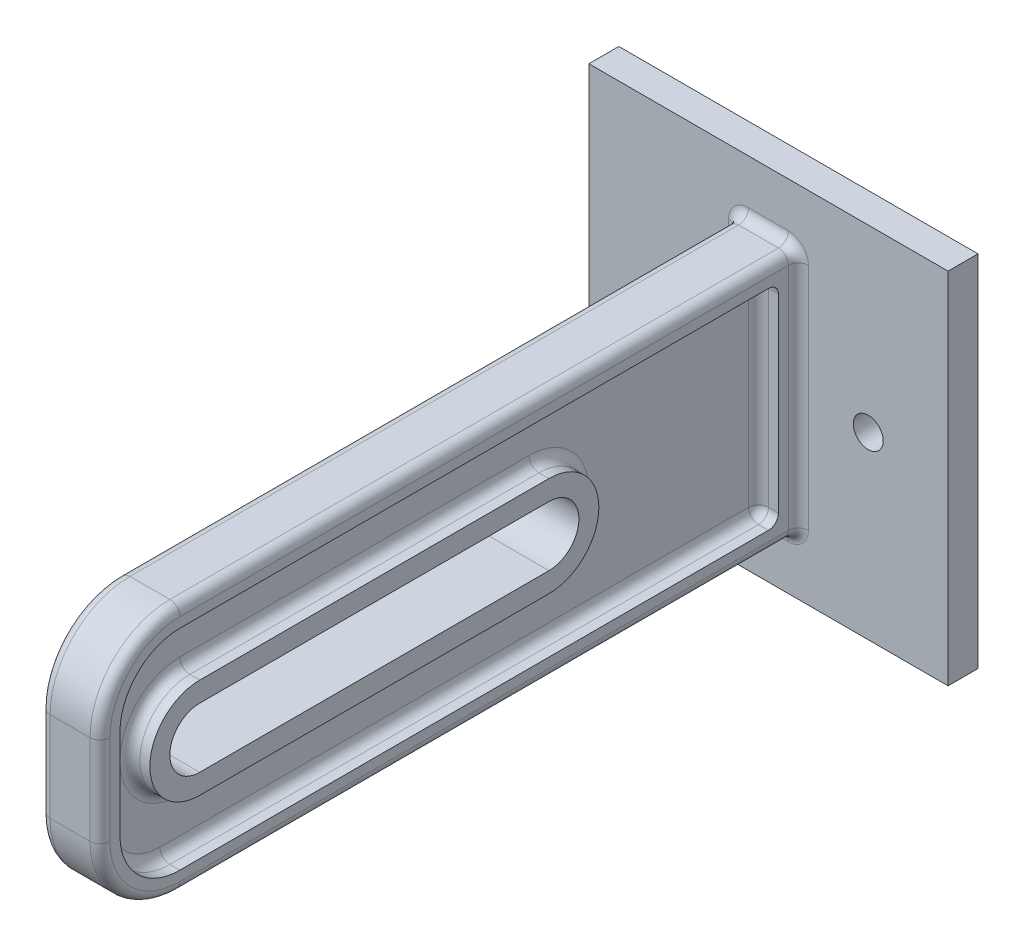
SolidWorks part; units mm, degrees
ref_plane "Front Plane" through (0, 0, 0) normal (0, 0, 1) x (1, 0, 0)
ref_plane "Top Plane" through (0, 0, 0) normal (0, 1, 0) x (1, 0, 0)
ref_plane "Right Plane" through (0, 0, 0) normal (1, 0, 0) x (0, 0, -1)
sketch "Sketch1" plane through (0, 0, 0) normal (0, 0, 1) x (1, 0, 0)
  line L1 (-18, -18) -> (18, -18)
  line L2 (-18, -18) -> (-18, 18)
  line L3 (-18, 18) -> (18, 18)
  line L4 (18, -18) -> (18, 18)
  line L5 (-18, -18) -> (18, 18) construction
  line L6 (-18, 18) -> (18, -18) construction
  point P0 (0, 0)
  dimension "D1" = 36
extrude "Boss-Extrude1" add sketch "Sketch1" along normal blind 3
sketch "Sketch2" plane through (0, 0, 3) normal (0, 0, 1) x (1, 0, 0)
  line L0 (-18, 0) -> (18, 0) construction
  line L1 (-18, 18) -> (-18, -18) construction
  line L2 (18, -18) -> (18, 18) construction
  circle A0 centre (-10, 0) radius 1.5
  circle A1 centre (10, 0) radius 1.5
  dimension "D1" = 3
  dimension "D2" = 20
  dimension "D3" = 10
extrude "Cut-Extrude1" cut sketch "Sketch2" against normal blind 3
sketch "Sketch3" plane through (0, 0, 3) normal (0, 0, 1) x (1, 0, 0)
  line L0 (-3, 12.5) -> (3, -12.5) construction
  line L1 (-3, 12.5) -> (3, 12.5)
  line L2 (-3, 12.5) -> (-3, -12.5)
  line L3 (-3, -12.5) -> (3, -12.5)
  line L4 (3, 12.5) -> (3, -12.5)
  line L5 (18, -18) -> (18, 18) construction
  line L6 (18, 18) -> (-18, 18) construction
  point P4 (0, 0)
  point P7 (18, 0)
  point P10 (0, 18)
  dimension "D1" = 25
  dimension "D2" = 6
extrude "Boss-Extrude2" add sketch "Sketch3" along normal blind 70
sketch "Sketch4" plane through (3, 0, 0) normal (1, 0, 0) x (0, 0, -1)
  line L0 (-63, 0) -> (-28, 0) construction
  line L1 (-63, 3) -> (-28, 3)
  line L2 (-63, -3) -> (-28, -3)
  line L3 (-73, -12.5) -> (-73, 12.5) construction
  arc A0 (-63, 3) -> (-63, -3) centre (-63, 0) ccw
  arc A1 (-28, -3) -> (-28, 3) centre (-28, 0) ccw
  point P3 (-45.5, 0)
  dimension "D1" = 3
  dimension "D2" = 35
  dimension "D3" = 10
extrude "Cut-Extrude2" cut sketch "Sketch4" against normal blind 70
fillet "Fillet1" radius 8 2 edges at (0, 12.5, 73) (0, -12.5, 73)
sketch "Sketch5" plane through (3, 0, 0) normal (1, 0, 0) x (0, 0, -1)
  line L8 (-5, 10.5) -> (-65, 10.5)
  line L9 (-71, 4.5) -> (-71, -4.5)
  line L10 (-65, -10.5) -> (-5, -10.5)
  line L11 (-5, -10.5) -> (-5, 10.5)
  line L12 (-5, 10.5) -> (-65, 10.5)
  line L13 (-71, 4.5) -> (-71, -4.5)
  line L14 (-65, -10.5) -> (-5, -10.5)
  line L15 (-5, -10.5) -> (-5, 10.5)
  line L20 (-28, 5) -> (-63, 5)
  line L21 (-63, -5) -> (-28, -5)
  line L22 (-28, 5) -> (-63, 5)
  line L23 (-63, -5) -> (-28, -5)
  arc A4 (-65, 10.5) -> (-71, 4.5) centre (-65, 4.5) ccw
  arc A5 (-71, -4.5) -> (-65, -10.5) centre (-65, -4.5) ccw
  arc A6 (-65, 10.5) -> (-71, 4.5) centre (-65, 4.5) ccw
  arc A7 (-71, -4.5) -> (-65, -10.5) centre (-65, -4.5) ccw
  arc A12 (-28, -5) -> (-28, 5) centre (-28, 0) ccw
  arc A13 (-63, 5) -> (-63, -5) centre (-63, 0) ccw
  arc A14 (-28, -5) -> (-28, 5) centre (-28, 0) ccw
  arc A15 (-63, 5) -> (-63, -5) centre (-63, 0) ccw
  dimension "D1" = 2
  dimension "D2" = 2
extrude "Cut-Extrude3" cut sketch "Sketch5" against normal blind 2
mirror "Mirror1" about plane through (0, 0, 0) normal (1, 0, 0) of "Cut-Extrude3"
fillet "Fillet2" radius 1 14 edges at (3, 12.5, 34) (3, 10.1569, 70.6569) (3, 0, 73) (3, -10.1569, 70.6569) (-3, -10.1569, 70.6569) (-3, -12.5, 34) (-3, 0, 3) (-3, 12.5, 34) (-3, 10.1569, 70.6569) (-3, 0, 73) (3, -12.5, 34) (0, -12.5, 3) (0, 12.5, 3) (3, 0, 3)
fillet "Fillet4" radius 1 8 edges at (1, -10.5, 35) (1, -8.7426, 69.2426) (1, 0, 71) (1, 8.7426, 69.2426) (1, 10.5, 35) (2, 10.5, 5) (2, -10.5, 5) (1, 0, 5)
fillet "Fillet5" radius 1 4 edges at (1, 0, 68) (1, 5, 45.5) (1, 0, 23) (1, -5, 45.5)
fillet "Fillet6" radius 1 8 edges at (-1, -10.5, 35) (-1, -8.7426, 69.2426) (-1, 0, 71) (-1, 8.7426, 69.2426) (-2, -10.5, 5) (-2, 10.5, 5) (-1, 0, 5) (-1, 10.5, 35)
fillet "Fillet7" radius 1 4 edges at (-1, 0, 68) (-1, 5, 45.5) (-1, 0, 23) (-1, -5, 45.5)
